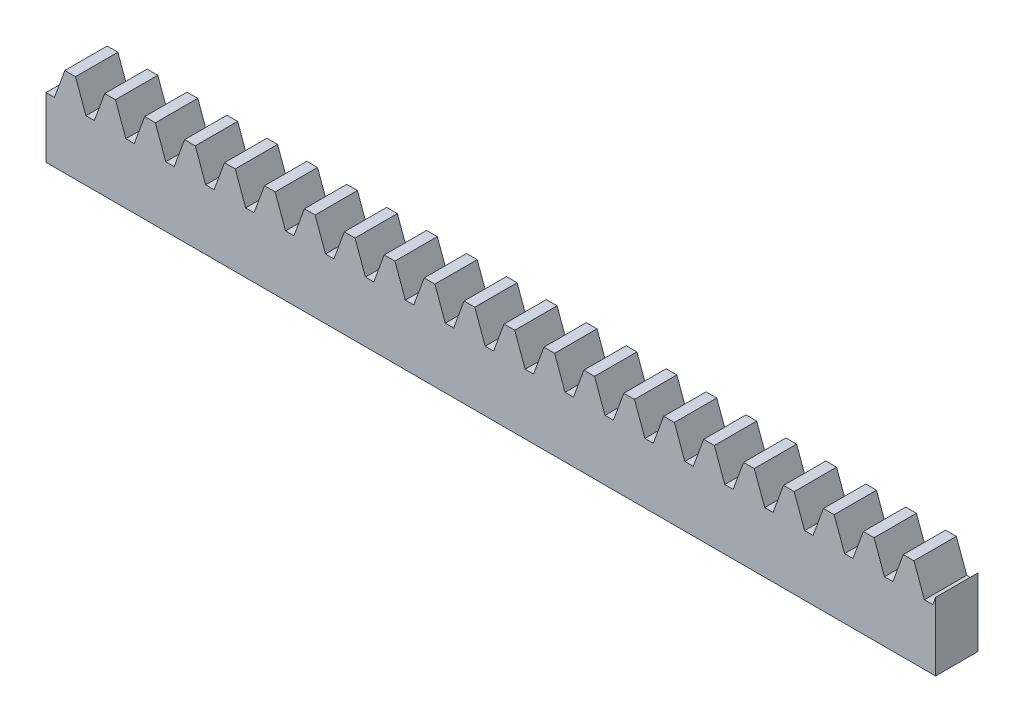
SolidWorks part; units mm, degrees
ref_plane "Front Plane" through (0, 0, 0) normal (0, 0, 1) x (1, 0, 0)
ref_plane "Top Plane" through (0, 0, 0) normal (0, 1, 0) x (1, 0, 0)
ref_plane "Right Plane" through (0, 0, 0) normal (1, 0, 0) x (0, 0, -1)
ref_plane "Plane1" through (0, 0, 0) normal (0, 0, -1) x (-1, 0, 0)
sketch "Sketch1" plane through (0, 0, 0) normal (0, 0, -1) x (-1, 0, 0)
  line L0 (-105, -1.9029) -> (-105, -8)
  line L1 (-105, -8) -> (105, -8)
  line L2 (105, -8) -> (105, -3.75)
  line L3 (105, -3.75) -> (103.0174, -3.75)
  line L4 (103.0174, -3.75) -> (100.5606, 3)
  line L5 (100.5606, 3) -> (98.032, 3)
  line L6 (98.032, 3) -> (95.5752, -3.75)
  line L7 (95.5752, -3.75) -> (93.5926, -3.75)
  line L8 (93.5926, -3.75) -> (91.1358, 3)
  line L9 (91.1358, 3) -> (88.6072, 3)
  line L10 (88.6072, 3) -> (86.1504, -3.75)
  line L11 (86.1504, -3.75) -> (84.1678, -3.75)
  line L12 (84.1678, -3.75) -> (81.711, 3)
  line L13 (81.711, 3) -> (79.1825, 3)
  line L14 (79.1825, 3) -> (76.7257, -3.75)
  line L15 (76.7257, -3.75) -> (74.7431, -3.75)
  line L16 (74.7431, -3.75) -> (72.2863, 3)
  line L17 (72.2863, 3) -> (69.7577, 3)
  line L18 (69.7577, 3) -> (67.3009, -3.75)
  line L19 (67.3009, -3.75) -> (65.3183, -3.75)
  line L20 (65.3183, -3.75) -> (62.8615, 3)
  line L21 (62.8615, 3) -> (60.3329, 3)
  line L22 (60.3329, 3) -> (57.8761, -3.75)
  line L23 (57.8761, -3.75) -> (55.8935, -3.75)
  line L24 (55.8935, -3.75) -> (53.4367, 3)
  line L25 (53.4367, 3) -> (50.9081, 3)
  line L26 (50.9081, 3) -> (48.4513, -3.75)
  line L27 (48.4513, -3.75) -> (46.4687, -3.75)
  line L28 (46.4687, -3.75) -> (44.0119, 3)
  line L29 (44.0119, 3) -> (41.4834, 3)
  line L30 (41.4834, 3) -> (39.0266, -3.75)
  line L31 (39.0266, -3.75) -> (37.0439, -3.75)
  line L32 (37.0439, -3.75) -> (34.5871, 3)
  line L33 (34.5871, 3) -> (32.0586, 3)
  line L34 (32.0586, 3) -> (29.6018, -3.75)
  line L35 (29.6018, -3.75) -> (27.6192, -3.75)
  line L36 (27.6192, -3.75) -> (25.1624, 3)
  line L37 (25.1624, 3) -> (22.6338, 3)
  line L38 (22.6338, 3) -> (20.177, -3.75)
  line L39 (20.177, -3.75) -> (18.1944, -3.75)
  line L40 (18.1944, -3.75) -> (15.7376, 3)
  line L41 (15.7376, 3) -> (13.209, 3)
  line L42 (13.209, 3) -> (10.7522, -3.75)
  line L43 (10.7522, -3.75) -> (8.7696, -3.75)
  line L44 (8.7696, -3.75) -> (6.3128, 3)
  line L45 (6.3128, 3) -> (3.7842, 3)
  line L46 (3.7842, 3) -> (1.3274, -3.75)
  line L47 (1.3274, -3.75) -> (-0.6552, -3.75)
  line L48 (-0.6552, -3.75) -> (-3.112, 3)
  line L49 (-3.112, 3) -> (-5.6405, 3)
  line L50 (-5.6405, 3) -> (-8.0973, -3.75)
  line L51 (-8.0973, -3.75) -> (-10.0799, -3.75)
  line L52 (-10.0799, -3.75) -> (-12.5367, 3)
  line L53 (-12.5367, 3) -> (-15.0653, 3)
  line L54 (-15.0653, 3) -> (-17.5221, -3.75)
  line L55 (-17.5221, -3.75) -> (-19.5047, -3.75)
  line L56 (-19.5047, -3.75) -> (-21.9615, 3)
  line L57 (-21.9615, 3) -> (-24.4901, 3)
  line L58 (-24.4901, 3) -> (-26.9469, -3.75)
  line L59 (-26.9469, -3.75) -> (-28.9295, -3.75)
  line L60 (-28.9295, -3.75) -> (-31.3863, 3)
  line L61 (-31.3863, 3) -> (-33.9149, 3)
  line L62 (-33.9149, 3) -> (-36.3717, -3.75)
  line L63 (-36.3717, -3.75) -> (-38.3543, -3.75)
  line L64 (-38.3543, -3.75) -> (-40.8111, 3)
  line L65 (-40.8111, 3) -> (-43.3396, 3)
  line L66 (-43.3396, 3) -> (-45.7964, -3.75)
  line L67 (-45.7964, -3.75) -> (-47.7791, -3.75)
  line L68 (-47.7791, -3.75) -> (-50.2359, 3)
  line L69 (-50.2359, 3) -> (-52.7644, 3)
  line L70 (-52.7644, 3) -> (-55.2212, -3.75)
  line L71 (-55.2212, -3.75) -> (-57.2038, -3.75)
  line L72 (-57.2038, -3.75) -> (-59.6606, 3)
  line L73 (-59.6606, 3) -> (-62.1892, 3)
  line L74 (-62.1892, 3) -> (-64.646, -3.75)
  line L75 (-64.646, -3.75) -> (-66.6286, -3.75)
  line L76 (-66.6286, -3.75) -> (-69.0854, 3)
  line L77 (-69.0854, 3) -> (-71.614, 3)
  line L78 (-71.614, 3) -> (-74.0708, -3.75)
  line L79 (-74.0708, -3.75) -> (-76.0534, -3.75)
  line L80 (-76.0534, -3.75) -> (-78.5102, 3)
  line L81 (-78.5102, 3) -> (-81.0388, 3)
  line L82 (-81.0388, 3) -> (-83.4956, -3.75)
  line L83 (-83.4956, -3.75) -> (-85.4782, -3.75)
  line L84 (-85.4782, -3.75) -> (-87.935, 3)
  line L85 (-87.935, 3) -> (-90.4635, 3)
  line L86 (-90.4635, 3) -> (-92.9203, -3.75)
  line L87 (-92.9203, -3.75) -> (-94.9029, -3.75)
  line L88 (-94.9029, -3.75) -> (-97.3597, 3)
  line L89 (-97.3597, 3) -> (-99.8883, 3)
  line L90 (-99.8883, 3) -> (-102.3451, -3.75)
  line L91 (-102.3451, -3.75) -> (-104.3277, -3.75)
  line L92 (-104.3277, -3.75) -> (-105, -1.9029)
extrude "Boss-Extrude1" add sketch "Sketch1" against normal blind 10
sketch "Sketch3" plane through (0, -8, 0) normal (0, -1, 0) x (1, 0, 0)
  line L1 (-105, 10) -> (105, 10)
  line L2 (-105, 10) -> (-105, 0)
  line L3 (-105, 0) -> (105, 0)
  line L4 (105, 10) -> (105, 0)
extrude "Boss-Extrude2" add sketch "Sketch3" along normal blind 10
sketch "Sketch4" plane through (-105, 0, 0) normal (-1, 0, 0) x (0, 0, 1)
  line L1 (0, -18) -> (0, -3.75) construction
  line L3 (10, -18) -> (0, -18) construction
  circle A0 centre (5, -10.9) radius 1
  dimension "D1" = 2
  dimension "D2" = 5
  dimension "D3" = 7.1
extrude "Cut-Extrude1" cut sketch "Sketch4" against normal blind 10 contours A0
